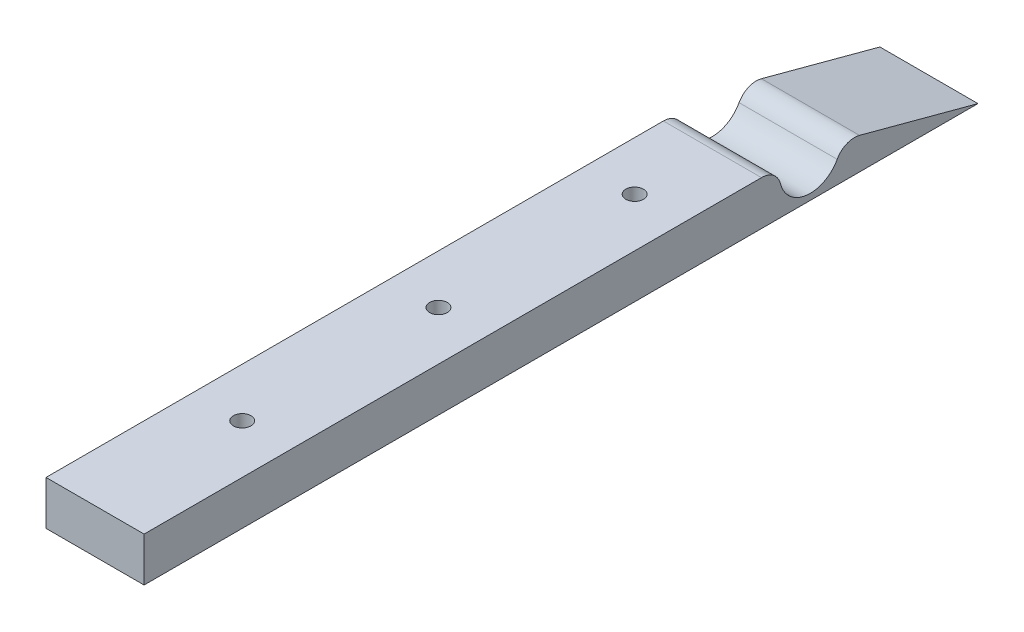
SolidWorks part; units mm, degrees
ref_plane "Front Plane" through (0, 0, 0) normal (0, 0, 1) x (1, 0, 0)
ref_plane "Top Plane" through (0, 0, 0) normal (0, 1, 0) x (1, 0, 0)
ref_plane "Right Plane" through (0, 0, 0) normal (1, 0, 0) x (0, 0, -1)
sketch "Sketch1" plane through (0, 0, 0) normal (1, 0, 0) x (0, 0, -1)
  line L0 (0, 0) -> (215.9, 0)
  line L1 (0, 0) -> (0, 11.43)
  line L2 (0, 11.43) -> (159.8416, 11.43)
  line L3 (215.9, 0) -> (185.2208, 8.2205)
  arc A0 (164.7682, 7.589) -> (179.4416, 5.7375) centre (172.466, 9.525) ccw
  arc A1 (159.8416, 11.43) -> (164.7682, 7.589) centre (159.8416, 6.35) cw
  arc A2 (185.2208, 8.2205) -> (179.4416, 5.7375) centre (183.906, 3.3136) ccw
  point P7 (172.466, 1.5875)
  dimension "D2" = 11.43
  dimension "D4" = 15.875
  dimension "D7" = 5.08
  dimension "D1" = 215.9
  dimension "D3" = 15
  dimension "D5" = 1.5875
  dimension "D6" = 43.434
extrude "Boss-Extrude1" add sketch "Sketch1" along normal blind 25.4
sketch "Sketch2" plane through (0, 0, 0) normal (0, -1, 0) x (1, 0, 0)
  line L0 (12.7, -215.9) -> (12.7, -139.7) construction
  line L1 (25.4, -215.9) -> (0, -215.9) construction
  circle A0 centre (12.7, -139.7) radius 2.286
  circle A1 centre (12.7, -88.9) radius 2.286
  circle A2 centre (12.7, -38.1) radius 2.286
  dimension "D2" = 4.572
  dimension "D1" = 76.2
  dimension "D4" = 50.8
  dimension "D3" = 3
extrude "Cut-Extrude1" cut sketch "Sketch2" against normal through all
sketch "Sketch3" plane through (0, 0, 0) normal (0, -1, 0) x (1, 0, 0)
  line L0 (25.4, 0) -> (0, 0) construction
  line L1 (18.1259, -139.7) -> (15.413, -135.001)
  line L2 (15.413, -135.001) -> (9.987, -135.001)
  line L3 (9.987, -135.001) -> (7.2741, -139.7)
  line L4 (7.2741, -139.7) -> (9.987, -144.399)
  line L5 (9.987, -144.399) -> (15.413, -144.399)
  line L6 (15.413, -144.399) -> (18.1259, -139.7)
  line L7 (18.1259, -88.9) -> (15.413, -84.201)
  line L8 (15.413, -84.201) -> (9.987, -84.201)
  line L9 (9.987, -84.201) -> (7.2741, -88.9)
  line L10 (7.2741, -88.9) -> (9.987, -93.599)
  line L11 (9.987, -93.599) -> (15.413, -93.599)
  line L12 (15.413, -93.599) -> (18.1259, -88.9)
  line L13 (18.1259, -38.1) -> (15.413, -33.401)
  line L14 (15.413, -33.401) -> (9.987, -33.401)
  line L15 (9.987, -33.401) -> (7.2741, -38.1)
  line L16 (7.2741, -38.1) -> (9.987, -42.799)
  line L17 (9.987, -42.799) -> (15.413, -42.799)
  line L18 (15.413, -42.799) -> (18.1259, -38.1)
  circle A0 centre (12.7, -139.7) radius 4.699 construction
  circle A1 centre (12.7, -88.9) radius 4.699 construction
  circle A2 centre (12.7, -38.1) radius 4.699 construction
  dimension "D1" = 9.398
extrude "Cut-Extrude2" cut sketch "Sketch3" against normal blind 6.35
